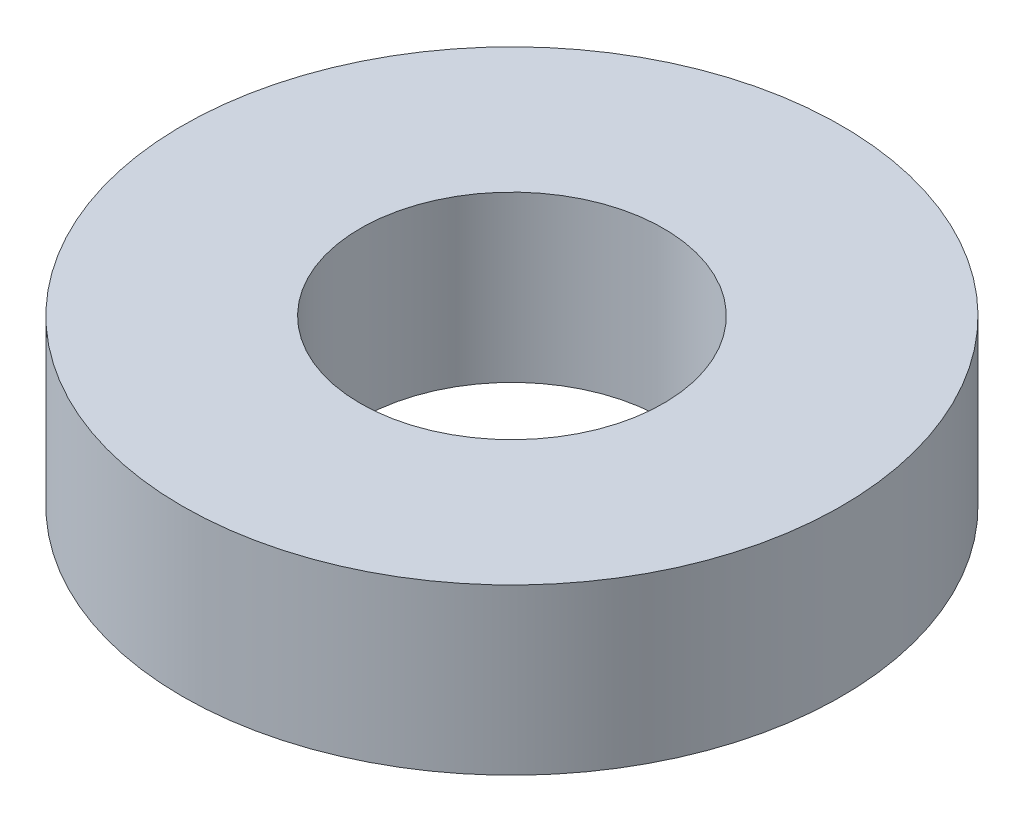
SolidWorks part; units mm, degrees
ref_plane "Front" through (0, 0, 0) normal (0, 0, 1) x (1, 0, 0)
ref_plane "Top" through (0, 0, 0) normal (0, 1, 0) x (1, 0, 0)
ref_plane "Right" through (0, 0, 0) normal (1, 0, 0) x (0, 0, -1)
sketch "Sketch1" plane through (0, 0, 0) normal (0, 1, 0) x (1, 0, 0)
  circle A0 centre (0, 0) radius 3.175
  circle A1 centre (0, 0) radius 1.4605
  dimension "D1" = 6.35
  dimension "D2" = 2.921
extrude "Boss-Extrude1" add sketch "Sketch1" along normal blind 1.5875
